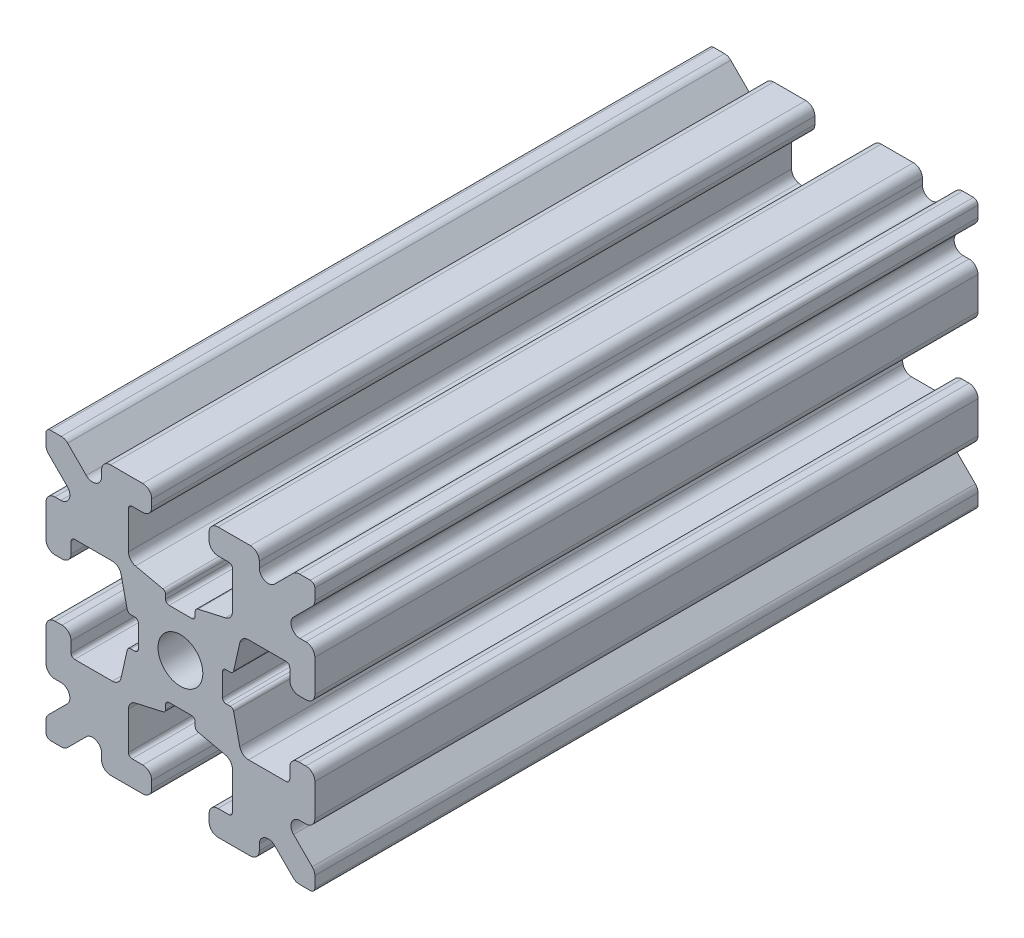
SolidWorks part; units mm, degrees
ref_plane "Front Plane" through (0, 0, 0) normal (0, 0, 1) x (1, 0, 0)
ref_plane "Top Plane" through (0, 0, 0) normal (0, 1, 0) x (1, 0, 0)
ref_plane "Right Plane" through (0, 0, 0) normal (1, 0, 0) x (0, 0, -1)
sketch "Sketch1" plane through (0, 0, 0) normal (0, 0, 1) x (1, 0, 0)
  line L1 (-7.5, -7.5) -> (7.5, -7.5)
  line L2 (-7.5, -7.5) -> (-7.5, 7.5)
  line L3 (-7.5, 7.5) -> (7.5, 7.5)
  line L4 (7.5, -7.5) -> (7.5, 7.5)
  line L5 (-7.5, -7.5) -> (7.5, 7.5) construction
  line L6 (-7.5, 7.5) -> (7.5, -7.5) construction
  circle A0 centre (0, 0) radius 1.25
  point P0 (0, 0)
  dimension "D2" = 2.5
  dimension "D1" = 15
extrude "Boss-Extrude1" add sketch "Sketch1" along normal mid plane 37
fillet "Fillet1" radius 0.25 4 edges at (7.5, -7.5, 0) (-7.5, -7.5, 0) (7.5, 7.5, 0) (-7.5, 7.5, 0)
sketch "Sketch2" plane through (0, 0, 18.5) normal (0, 0, 1) x (1, 0, 0)
  line L0 (-7.5, 7.25) -> (-7.5, -7.25) construction
  line L1 (-7.5, 1.6) -> (-6.1, 1.6)
  line L2 (-7.5, 1.6) -> (-7.5, -1.6)
  line L3 (-7.5, -1.6) -> (-6.1, -1.6)
  line L4 (-6.1, 1.6) -> (-6.1, 2.9)
  line L5 (0, 0) -> (-12.1036, 0) construction
  line L6 (-6.1, -2.9) -> (-3.4, -2.9)
  line L7 (0, 0) -> (-7.25, 7.25) construction
  line L8 (-6.1, 2.9) -> (-3.4, 2.9)
  line L9 (-3.4, -2.9) -> (-3.4, 2.9)
  line L10 (55, 0) -> (-55, 0) construction
  line L11 (-6.1, -2.9) -> (-6.1, -1.6)
  line L12 (2.9, 6.1) -> (1.6, 6.1)
  line L13 (2.9, 3.4) -> (-2.9, 3.4)
  line L14 (-2.9, 6.1) -> (-2.9, 3.4)
  line L15 (2.9, 6.1) -> (2.9, 3.4)
  line L16 (-1.6, 6.1) -> (-2.9, 6.1)
  line L17 (1.6, 7.5) -> (1.6, 6.1)
  line L18 (-1.6, 7.5) -> (1.6, 7.5)
  line L19 (-1.6, 7.5) -> (-1.6, 6.1)
  line L20 (-1.6, -7.5) -> (-1.6, -6.1)
  line L21 (-1.6, -7.5) -> (1.6, -7.5)
  line L22 (1.6, -7.5) -> (1.6, -6.1)
  line L23 (-1.6, -6.1) -> (-2.9, -6.1)
  line L24 (2.9, -6.1) -> (2.9, -3.4)
  line L25 (-2.9, -6.1) -> (-2.9, -3.4)
  line L26 (2.9, -3.4) -> (-2.9, -3.4)
  line L27 (2.9, -6.1) -> (1.6, -6.1)
  line L28 (6.1, -2.9) -> (6.1, -1.6)
  line L29 (3.4, -2.9) -> (3.4, 2.9)
  line L30 (6.1, 2.9) -> (3.4, 2.9)
  line L31 (6.1, -2.9) -> (3.4, -2.9)
  line L32 (6.1, 1.6) -> (6.1, 2.9)
  line L33 (7.5, -1.6) -> (6.1, -1.6)
  line L34 (7.5, 1.6) -> (7.5, -1.6)
  line L35 (7.5, 1.6) -> (6.1, 1.6)
  dimension "D1" = 3.2
  dimension "D2" = 5.8
  dimension "D3" = 1.4
  dimension "D4" = 2.7
extrude "Cut-Extrude1" cut sketch "Sketch2" against normal through all
sketch "Sketch4" plane through (0, 0, 18.5) normal (0, 0, 1) x (1, 0, 0)
  line L0 (-3.4, 2.9) -> (-2.75, 0)
  line L1 (55, 0) -> (-55, 0) construction
  line L2 (-2.75, 0) -> (-3.4, -2.9)
  line L3 (-3.4, -2.9) -> (-3.4, 2.9) construction
  line L4 (-3.4, 2.9) -> (-3.4, -2.9)
  line L5 (-2.9, 3.4) -> (0, 2.75)
  line L6 (0, 2.75) -> (2.9, 3.4)
  line L7 (2.9, 3.4) -> (-2.9, 3.4)
  line L8 (3.4, 2.9) -> (2.75, 0)
  line L9 (2.75, 0) -> (3.4, -2.9)
  line L10 (3.4, -2.9) -> (3.4, 2.9)
  line L11 (-2.9, -3.4) -> (0, -2.75)
  line L12 (0, -2.75) -> (2.9, -3.4)
  line L13 (2.9, -3.4) -> (-2.9, -3.4)
  circle A2 centre (0, 0) radius 2.75
  circle A3 centre (0, 0) radius 2.75 construction
  dimension "D1" = 1.5
extrude "Cut-Extrude3" cut sketch "Sketch4" against normal through all
fillet "Fillet3" radius 0.5 16 edges at (-6.1, -1.6, 0) (-7.5, -1.6, 0) (-6.1, 1.6, 0) (-7.5, 1.6, 0) (-1.6, -7.5, 0) (-1.6, -6.1, 0) (1.6, -7.5, 0) (1.6, -6.1, 0) (6.1, -1.6, 0) (7.5, -1.6, 0) (7.5, 1.6, 0) (6.1, 1.6, 0) (1.6, 7.5, 0) (1.6, 6.1, 0) (-1.6, 7.5, 0) (-1.6, 6.1, 0)
fillet "Fillet4" radius 0.5 8 edges at (-3.4, 2.9, 0) (-3.4, -2.9, 0) (2.9, -3.4, 0) (-2.9, -3.4, 0) (3.4, -2.9, 0) (3.4, 2.9, 0) (-2.9, 3.4, 0) (2.9, 3.4, 0)
fillet "Fillet5" radius 3 4 edges at (0, -2.75, 0) (2.75, 0, 0) (-2.75, 0, 0) (0, 2.75, 0)
fillet "Fillet6" radius 0.2 8 edges at (-2.9, -6.1, 0) (2.9, -6.1, 0) (6.1, -2.9, 0) (6.1, 2.9, 0) (2.9, 6.1, 0) (-2.9, 6.1, 0) (-6.1, -2.9, 0) (-6.1, 2.9, 0)
sketch "Sketch5" plane through (0, 0, 18.5) normal (0, 0, 1) x (1, 0, 0)
  line L0 (0, 0) -> (-7.25, 7.25) construction
  line L1 (-7.5, 6.4393) -> (-5.4607, 4.4)
  line L2 (-6.4393, 7.5) -> (-4.4, 5.4607)
  line L3 (-7.5, 4.4) -> (-5.4607, 4.4)
  line L4 (-3.8003, 2.9) -> (-5.9, 2.9) construction
  line L5 (0, 0) -> (-12.1819, 0) construction
  line L6 (-4.4, 7.5) -> (-4.4, 5.4607)
  line L7 (-2.9, 5.9) -> (-2.9, 3.8003) construction
  line L8 (-7.5, 6.4393) -> (-7.5, 4.4)
  line L9 (-7.5, 7.25) -> (-7.5, 2.1) construction
  line L10 (2.1, -7.5) -> (7.25, -7.5) construction
  line L11 (7.5, -7.25) -> (7.5, -2.1) construction
  line L12 (7.25, 7.5) -> (2.1, 7.5) construction
  line L13 (-2.1, 7.5) -> (-7.25, 7.5) construction
  line L14 (-4.4, 7.5) -> (-6.4393, 7.5)
  line L16 (55, 0) -> (-55, 0) construction
  line L17 (0, 0) -> (0, 10.993) construction
  line L18 (0, -54.6431) -> (0, 54.6431) construction
  line L20 (4.4, 7.5) -> (6.4393, 7.5)
  line L22 (7.5, 6.4393) -> (7.5, 4.4)
  line L23 (4.4, 7.5) -> (4.4, 5.4607)
  line L24 (7.5, 4.4) -> (5.4607, 4.4)
  line L25 (6.4393, 7.5) -> (4.4, 5.4607)
  line L26 (7.5, 6.4393) -> (5.4607, 4.4)
  line L27 (7.5, -6.4393) -> (5.4607, -4.4)
  line L28 (6.4393, -7.5) -> (4.4, -5.4607)
  line L29 (7.5, -4.4) -> (5.4607, -4.4)
  line L30 (4.4, -7.5) -> (4.4, -5.4607)
  line L31 (7.5, -6.4393) -> (7.5, -4.4)
  line L33 (4.4, -7.5) -> (6.4393, -7.5)
  line L36 (-4.4, -7.5) -> (-6.4393, -7.5)
  line L38 (-7.5, -6.4393) -> (-7.5, -4.4)
  line L39 (-4.4, -7.5) -> (-4.4, -5.4607)
  line L40 (-7.5, -4.4) -> (-5.4607, -4.4)
  line L41 (-6.4393, -7.5) -> (-4.4, -5.4607)
  line L42 (-7.5, -6.4393) -> (-5.4607, -4.4)
  dimension "D1" = 1.5
  dimension "D2" = 1.5
  dimension "D3" = 1.5
extrude "Cut-Extrude4" cut sketch "Sketch5" against normal through all
fillet "Fillet8" radius 0.5 24 edges at (-5.4607, 4.4, 0) (-7.5, 4.4, 0) (-5.4607, -4.4, 0) (-7.5, -4.4, 0) (-4.4, -7.5, 0) (-4.4, -5.4607, 0) (4.4, -7.5, 0) (4.4, -5.4607, 0) (5.4607, -4.4, 0) (7.5, -4.4, 0) (7.5, 4.4, 0) (5.4607, 4.4, 0) (4.4, 5.4607, 0) (4.4, 7.5, 0) (-4.4, 5.4607, 0) (-4.4, 7.5, 0) (-6.4393, 7.5, 0) (-7.5, 6.4393, 0) (6.4393, 7.5, 0) (7.5, 6.4393, 0) (6.4393, -7.5, 0) (7.5, -6.4393, 0) (-6.4393, -7.5, 0) (-7.5, -6.4393, 0)
sketch "Sketch6" plane through (0, 0, 18.5) normal (0, 0, 1) x (1, 0, 0)
  line L0 (0, 0) -> (0, 11.013) construction
  line L1 (0.6561, 2.8971) -> (2.1235, 2.8971) construction
  line L2 (0, -54.6431) -> (0, 54.6431) construction
  line L3 (0, 0) -> (7.25, 7.25) construction
  line L4 (7.5, 0.8255) -> (7.5, -0.8255)
  line L5 (2.3471, 0.8255) -> (7.5, 0.8255)
  line L6 (0, 0) -> (12.4016, 0) construction
  line L7 (0.8255, -7.5) -> (-0.8255, -7.5)
  line L8 (2.3471, -0.8255) -> (2.3471, 0.8255)
  line L9 (0.8255, -2.3471) -> (0.8255, -7.5)
  line L10 (7.5, -0.8255) -> (2.3471, -0.8255)
  line L11 (-7.5, -0.8255) -> (-2.3471, -0.8255)
  line L12 (-2.3471, -0.8255) -> (-2.3471, 0.8255)
  line L13 (-0.8255, -2.3471) -> (0.8255, -2.3471)
  line L14 (-0.8255, 7.5) -> (-0.8255, 2.3471)
  line L15 (-0.8255, 2.3471) -> (0.8255, 2.3471)
  line L16 (-0.8255, -7.5) -> (-0.8255, -2.3471)
  line L17 (0.8255, 2.3471) -> (0.8255, 7.5)
  line L18 (0.8255, 7.5) -> (-0.8255, 7.5)
  line L19 (3.9, 7.5) -> (2.1, 7.5) construction
  line L20 (-2.3471, 0.8255) -> (-7.5, 0.8255)
  line L21 (-7.5, 0.8255) -> (-7.5, -0.8255)
  point P5 (0, -2.5973)
  point P7 (0, 2.5973)
  dimension "D3" = 0.55
  dimension "D1" = 1.651
extrude "Cut-Extrude5" cut sketch "Sketch6" against normal through all
fillet "Fillet10" radius 0.2 16 edges at (-2.935, 0.8255, 0) (-2.935, -0.8255, 0) (2.935, -0.8255, 0) (2.935, 0.8255, 0) (0.8255, 2.935, 0) (-0.8255, 2.935, 0) (-2.3471, 0.8255, 0) (-2.3471, -0.8255, 0) (0.8255, 2.3471, 0) (-0.8255, 2.3471, 0) (2.3471, 0.8255, 0) (2.3471, -0.8255, 0) (0.8255, -2.935, 0) (0.8255, -2.3471, 0) (-0.8255, -2.3471, 0) (-0.8255, -2.935, 0)
